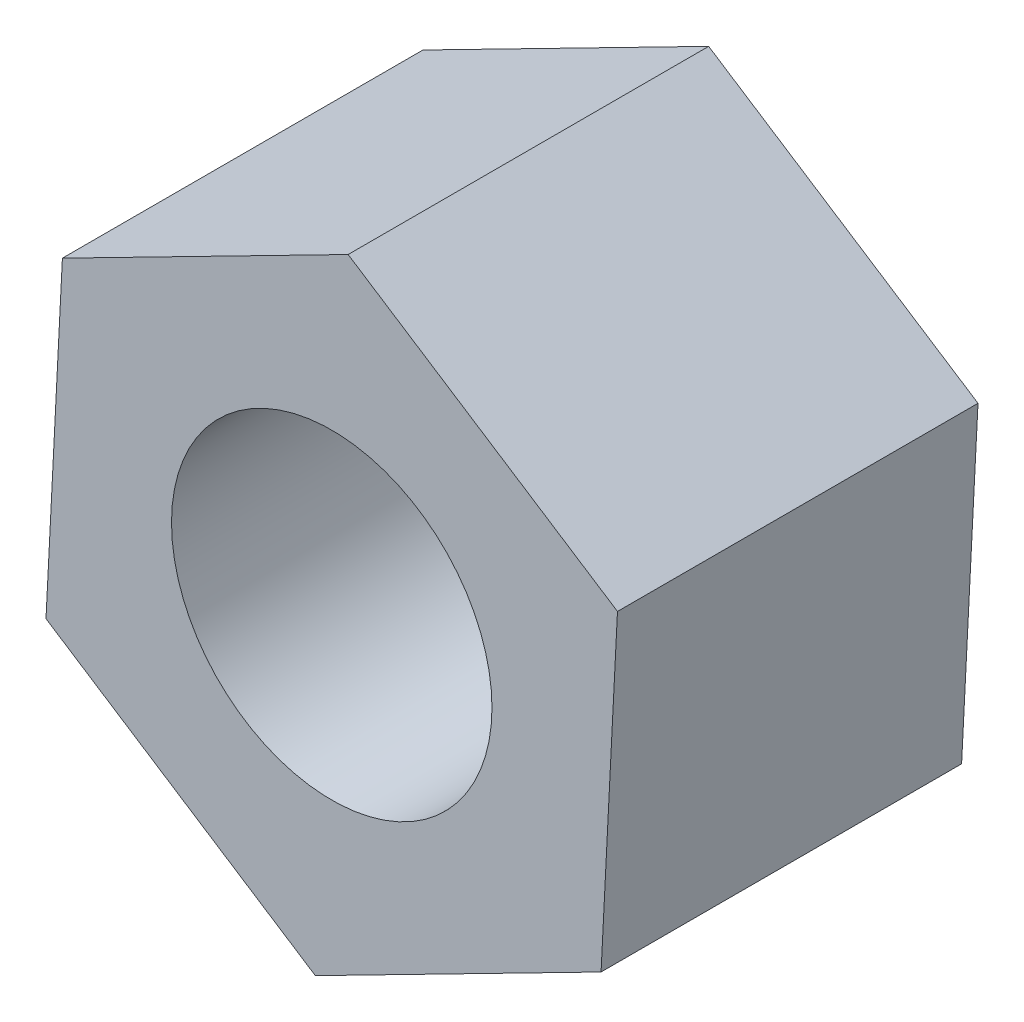
SolidWorks part; units mm, degrees
ref_plane "Front Plane" through (0, 0, 0) normal (0, 0, 1) x (1, 0, 0)
ref_plane "Top Plane" through (0, 0, 0) normal (0, 1, 0) x (1, 0, 0)
ref_plane "Right Plane" through (0, 0, 0) normal (1, 0, 0) x (0, 0, -1)
sketch "Sketch1" plane through (0, 0, 0) normal (0, 0, 1) x (1, 0, 0)
  line L1 (6.7234, -4.3547) -> (7.133, 3.6453)
  line L2 (7.133, 3.6453) -> (0.4096, 8)
  line L3 (0.4096, 8) -> (-6.7234, 4.3547)
  line L4 (-6.7234, 4.3547) -> (-7.133, -3.6453)
  line L5 (-7.133, -3.6453) -> (-0.4096, -8)
  line L6 (-0.4096, -8) -> (6.7234, -4.3547)
  circle A0 centre (0, 0) radius 6.9373 construction
  dimension "D1" = 8
extrude "Boss-Extrude1" add sketch "Sketch1" along normal mid plane 9
sketch "Sketch2" plane through (0, 0, -4.5) normal (0, 0, -1) x (-1, 0, 0)
  circle A0 centre (0, 0) radius 4
  dimension "D1" = 8
extrude "Cut-Extrude1" cut sketch "Sketch2" against normal blind 9
